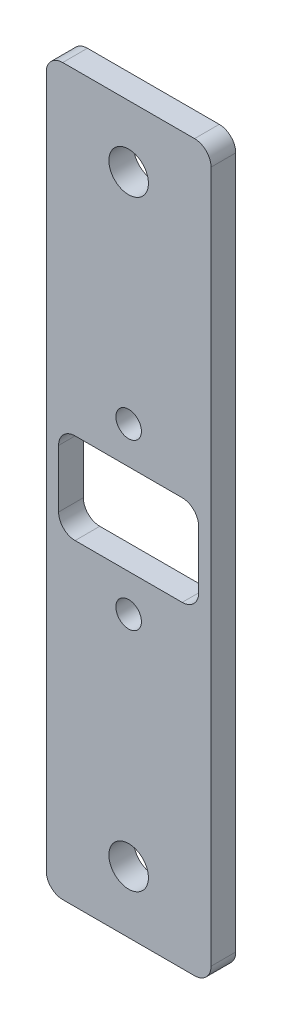
SolidWorks part; units mm, degrees
ref_plane "正面" through (0, 0, 0) normal (1, 0, 0) x (0, 1, 0)
ref_plane "平面" through (0, 0, 0) normal (0, 0, 1) x (0, 1, 0)
ref_plane "右側面" through (0, 0, 0) normal (0, 1, 0) x (-1, 0, 0)
sketch "ｽｹｯﾁ1" plane through (0, 0, 0) normal (0, 0, 1) x (0, 1, 0)
  line L1 (0, 0) -> (88, 0)
  line L2 (0, 0) -> (0, 20)
  line L3 (0, 20) -> (88, 20)
  line L4 (88, 0) -> (88, 20)
  line L5 (0, 0) -> (88, 20) construction
  line L6 (0, 20) -> (88, 0) construction
  line L7 (38.5, 1.5) -> (49.5, 1.5)
  line L8 (38.5, 1.5) -> (38.5, 18.5)
  line L9 (38.5, 18.5) -> (49.5, 18.5)
  line L10 (49.5, 1.5) -> (49.5, 18.5)
  line L11 (38.5, 1.5) -> (49.5, 18.5) construction
  line L12 (38.5, 18.5) -> (49.5, 1.5) construction
  circle A0 centre (7.5, 10) radius 2.4
  circle A1 centre (80.5, 10) radius 2.4
  circle A2 centre (54, 10) radius 1.55
  circle A3 centre (34, 10) radius 1.55
  point P4 (44, 10)
  point P6 (44, 0)
  point P7 (44, 10)
  point P20 (0, 10)
  dimension "D7" = 4.8
  dimension "D8" = 3.1
  dimension "D10" = 10
  dimension "D1" = 20
  dimension "D2" = 88
  dimension "D3" = 11
  dimension "D4" = 17
  dimension "D5" = 73
  dimension "D6" = 36.5
  dimension "D9" = 20
extrude "ﾎﾞｽ - 押し出し1" add sketch "ｽｹｯﾁ1" along normal blind 3
fillet "ﾌｨﾚｯﾄ1" radius 2 8 edges at (-1.5, 38.5, 1.5) (-1.5, 49.5, 1.5) (-18.5, 49.5, 1.5) (-18.5, 38.5, 1.5) (0, 88, 1.5) (-20, 88, 1.5) (-20, 0, 1.5) (0, 0, 1.5)
